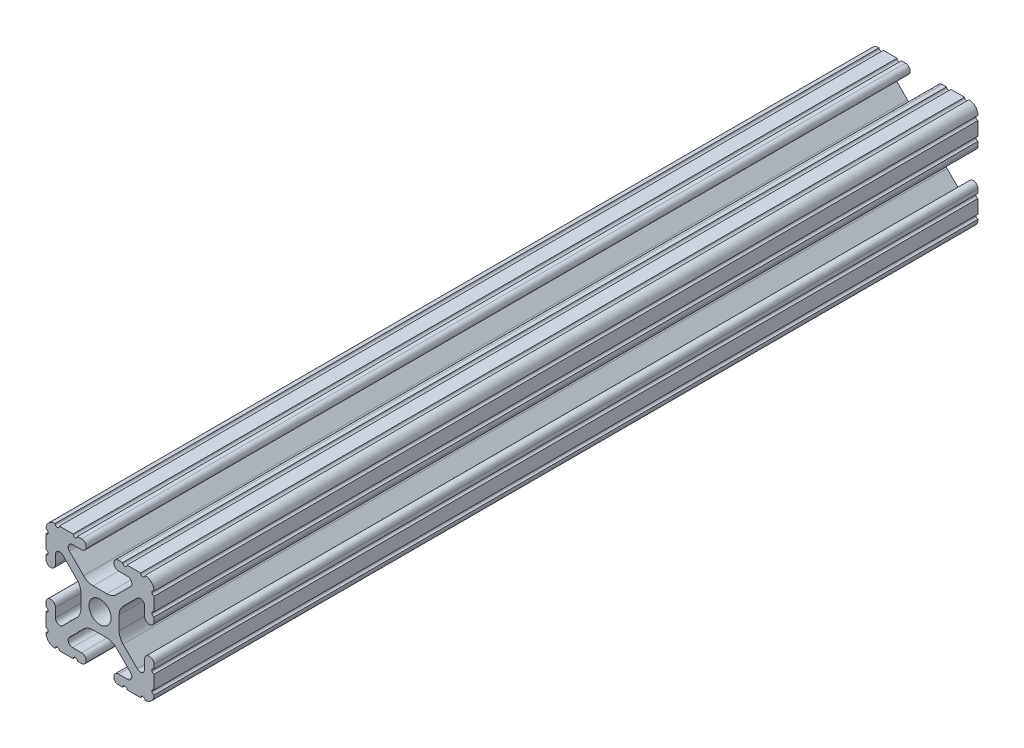
SolidWorks part; units mm, degrees
material "6061-T6 (SS)"
ref_plane "Front Plane" through (0, 0, 0) normal (0, 0, 1) x (1, 0, 0)
ref_plane "Top Plane" through (0, 0, 0) normal (0, 1, 0) x (1, 0, 0)
ref_plane "Right Plane" through (0, 0, 0) normal (1, 0, 0) x (0, 0, -1)
ref_plane "Plane1" through (0, 0, -450.85) normal (0, 0, -1) x (-1, 0, 0)
sketch "Sketch1" plane through (0, 0, -450.85) normal (0, 0, -1) x (-1, 0, 0)
  line L0 (12.7, -9.5504) -> (12.7, -6.3331)
  line L1 (12.7, -5.3171) -> (12.7, -4.3434)
  line L2 (10.4902, -4.3434) -> (10.4902, -6.4748)
  line L3 (8.7558, -7.1932) -> (5.4257, -3.8632)
  line L4 (4.4958, -1.6181) -> (4.4958, 1.6181)
  line L5 (5.4257, 3.8632) -> (8.7558, 7.1932)
  line L6 (10.4902, 6.4748) -> (10.4902, 4.3434)
  line L7 (12.7, 4.3434) -> (12.7, 5.3171)
  line L8 (12.7, 6.3331) -> (12.7, 9.5504)
  line L9 (9.5504, 12.7) -> (6.3331, 12.7)
  line L10 (5.3171, 12.7) -> (4.3434, 12.7)
  line L11 (4.3434, 10.4902) -> (6.4748, 10.4902)
  line L12 (7.1932, 8.7558) -> (3.8632, 5.4257)
  line L13 (1.6181, 4.4958) -> (-1.6181, 4.4958)
  line L14 (-3.8632, 5.4257) -> (-7.1932, 8.7558)
  line L15 (-6.4748, 10.4902) -> (-4.3434, 10.4902)
  line L16 (-4.3434, 12.7) -> (-5.3171, 12.7)
  line L17 (-6.3331, 12.7) -> (-9.5504, 12.7)
  line L18 (-12.7, 9.5504) -> (-12.7, 6.3331)
  line L19 (-12.7, 5.3171) -> (-12.7, 4.3434)
  line L20 (-10.4902, 4.3434) -> (-10.4902, 6.4748)
  line L21 (-8.7558, 7.1932) -> (-5.4257, 3.8632)
  line L22 (-4.4958, 1.6181) -> (-4.4958, -1.6181)
  line L23 (-5.4257, -3.8632) -> (-8.7558, -7.1932)
  line L24 (-10.4902, -6.4748) -> (-10.4902, -4.3434)
  line L25 (-12.7, -4.3434) -> (-12.7, -5.3171)
  line L26 (-12.7, -6.3331) -> (-12.7, -9.5504)
  line L27 (-9.5504, -12.7) -> (-6.3331, -12.7)
  line L28 (-5.3171, -12.7) -> (-4.3434, -12.7)
  line L29 (-4.3434, -10.4902) -> (-6.4748, -10.4902)
  line L30 (-7.1932, -8.7558) -> (-3.8632, -5.4257)
  line L31 (-1.6181, -4.4958) -> (1.6181, -4.4958)
  line L32 (3.8632, -5.4257) -> (7.1932, -8.7558)
  line L33 (6.4748, -10.4902) -> (4.3434, -10.4902)
  line L34 (4.3434, -12.7) -> (5.3171, -12.7)
  line L35 (6.3331, -12.7) -> (9.5504, -12.7)
  arc A0 (12.6998, -10.5664) -> (12.7, -9.5504) centre (12.7, -10.0584) cw
  arc A1 (12.7, -6.3331) -> (12.7, -5.3171) centre (12.7, -5.8251) cw
  arc A2 (12.7, -4.3434) -> (10.4902, -4.3434) centre (11.5951, -4.3434) ccw
  arc A3 (10.4902, -6.4748) -> (8.7558, -7.1932) centre (9.4742, -6.4748) cw
  arc A4 (5.4257, -3.8632) -> (4.4958, -1.6181) centre (7.6708, -1.6181) cw
  arc A5 (4.4958, 1.6181) -> (5.4257, 3.8632) centre (7.6708, 1.6181) cw
  arc A6 (8.7558, 7.1932) -> (10.4902, 6.4748) centre (9.4742, 6.4748) cw
  arc A7 (10.4902, 4.3434) -> (12.7, 4.3434) centre (11.5951, 4.3434) ccw
  arc A8 (12.7, 5.3171) -> (12.7, 6.3331) centre (12.7, 5.8251) cw
  arc A9 (12.7, 9.5504) -> (12.6998, 10.5664) centre (12.7, 10.0584) cw
  arc A10 (12.6998, 10.5664) -> (10.5664, 12.6998) centre (10.5918, 10.5918) ccw
  arc A11 (10.5664, 12.6998) -> (9.5504, 12.7) centre (10.0584, 12.7) cw
  arc A12 (6.3331, 12.7) -> (5.3171, 12.7) centre (5.8251, 12.7) cw
  arc A13 (4.3434, 12.7) -> (4.3434, 10.4902) centre (4.3434, 11.5951) ccw
  arc A14 (6.4748, 10.4902) -> (7.1932, 8.7558) centre (6.4748, 9.4742) cw
  arc A15 (3.8632, 5.4257) -> (1.6181, 4.4958) centre (1.6181, 7.6708) cw
  arc A16 (-1.6181, 4.4958) -> (-3.8632, 5.4257) centre (-1.6181, 7.6708) cw
  arc A17 (-7.1932, 8.7558) -> (-6.4748, 10.4902) centre (-6.4748, 9.4742) cw
  arc A18 (-4.3434, 10.4902) -> (-4.3434, 12.7) centre (-4.3434, 11.5951) ccw
  arc A19 (-5.3171, 12.7) -> (-6.3331, 12.7) centre (-5.8251, 12.7) cw
  arc A20 (-9.5504, 12.7) -> (-10.5664, 12.6998) centre (-10.0584, 12.7) cw
  arc A21 (-10.5664, 12.6998) -> (-12.6998, 10.5664) centre (-10.5918, 10.5918) ccw
  arc A22 (-12.6998, 10.5664) -> (-12.7, 9.5504) centre (-12.7, 10.0584) cw
  arc A23 (-12.7, 6.3331) -> (-12.7, 5.3171) centre (-12.7, 5.8251) cw
  arc A24 (-12.7, 4.3434) -> (-10.4902, 4.3434) centre (-11.5951, 4.3434) ccw
  arc A25 (-10.4902, 6.4748) -> (-8.7558, 7.1932) centre (-9.4742, 6.4748) cw
  arc A26 (-5.4257, 3.8632) -> (-4.4958, 1.6181) centre (-7.6708, 1.6181) cw
  arc A27 (-4.4958, -1.6181) -> (-5.4257, -3.8632) centre (-7.6708, -1.6181) cw
  arc A28 (-8.7558, -7.1932) -> (-10.4902, -6.4748) centre (-9.4742, -6.4748) cw
  arc A29 (-10.4902, -4.3434) -> (-12.7, -4.3434) centre (-11.5951, -4.3434) ccw
  arc A30 (-12.7, -5.3171) -> (-12.7, -6.3331) centre (-12.7, -5.8251) cw
  arc A31 (-12.7, -9.5504) -> (-12.6998, -10.5664) centre (-12.7, -10.0584) cw
  arc A32 (-12.6998, -10.5664) -> (-10.5664, -12.6998) centre (-10.5918, -10.5918) ccw
  arc A33 (-10.5664, -12.6998) -> (-9.5504, -12.7) centre (-10.0584, -12.7) cw
  arc A34 (-6.3331, -12.7) -> (-5.3171, -12.7) centre (-5.8251, -12.7) cw
  arc A35 (-4.3434, -12.7) -> (-4.3434, -10.4902) centre (-4.3434, -11.5951) ccw
  arc A36 (-6.4748, -10.4902) -> (-7.1932, -8.7558) centre (-6.4748, -9.4742) cw
  arc A37 (-3.8632, -5.4257) -> (-1.6181, -4.4958) centre (-1.6181, -7.6708) cw
  arc A38 (1.6181, -4.4958) -> (3.8632, -5.4257) centre (1.6181, -7.6708) cw
  arc A39 (7.1932, -8.7558) -> (6.4748, -10.4902) centre (6.4748, -9.4742) cw
  arc A40 (4.3434, -10.4902) -> (4.3434, -12.7) centre (4.3434, -11.5951) ccw
  arc A41 (5.3171, -12.7) -> (6.3331, -12.7) centre (5.8251, -12.7) cw
  arc A42 (9.5504, -12.7) -> (10.5664, -12.6998) centre (10.0584, -12.7) cw
  arc A43 (10.5664, -12.6998) -> (12.6998, -10.5664) centre (10.5918, -10.5918) ccw
  circle A44 centre (0, 0) radius 2.6035
extrude "Boss-Extrude1" add sketch "Sketch1" against normal mid plane 193.7512
